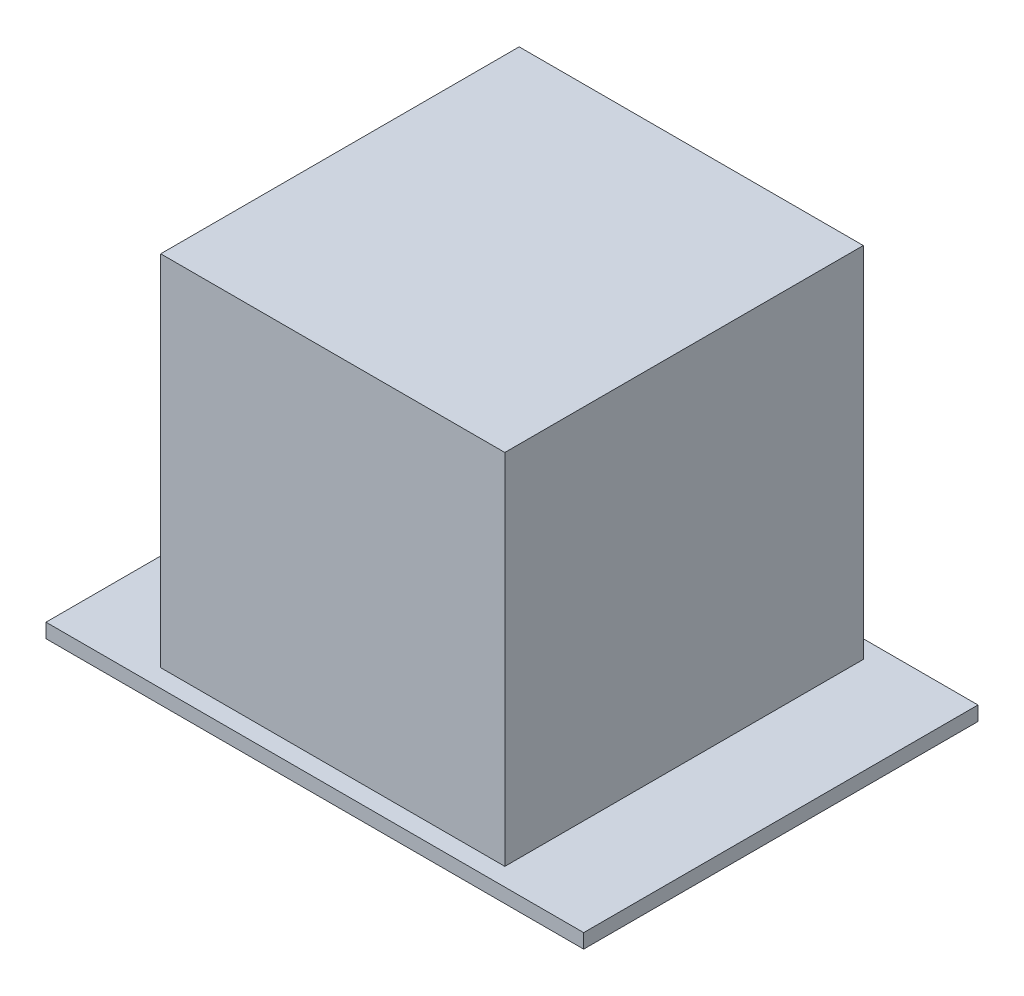
SolidWorks part; units mm, degrees
ref_plane "Front Plane" through (0, 0, 0) normal (0, 0, 1) x (1, 0, 0)
ref_plane "Top Plane" through (0, 0, 0) normal (0, 1, 0) x (1, 0, 0)
ref_plane "Right Plane" through (0, 0, 0) normal (1, 0, 0) x (0, 0, -1)
sketch "Sketch1" plane through (0, 0, 0) normal (0, 1, 0) x (1, 0, 0)
  line L1 (0, 0) -> (150, 0)
  line L2 (0, 0) -> (0, 110)
  line L3 (0, 110) -> (150, 110)
  line L4 (150, 0) -> (150, 110)
  dimension "D1" = 110
  dimension "D2" = 150
extrude "Boss-Extrude1" add sketch "Sketch1" along normal blind 4
sketch "Sketch2" plane through (0, 4, 0) normal (0, 1, 0) x (1, 0, 0)
  line L0 (0, 0) -> (150, 0) construction
  line L1 (27, 105) -> (123, 105)
  line L2 (27, 105) -> (27, 5)
  line L3 (27, 5) -> (123, 5)
  line L4 (123, 105) -> (123, 5)
  line L5 (150, 110) -> (0, 110) construction
  line L6 (150, 0) -> (150, 110) construction
  line L7 (0, 110) -> (0, 0) construction
  dimension "D1" = 5
  dimension "D2" = 5
  dimension "D3" = 27
  dimension "D4" = 27
extrude "Boss-Extrude2" add sketch "Sketch2" along normal blind 100
